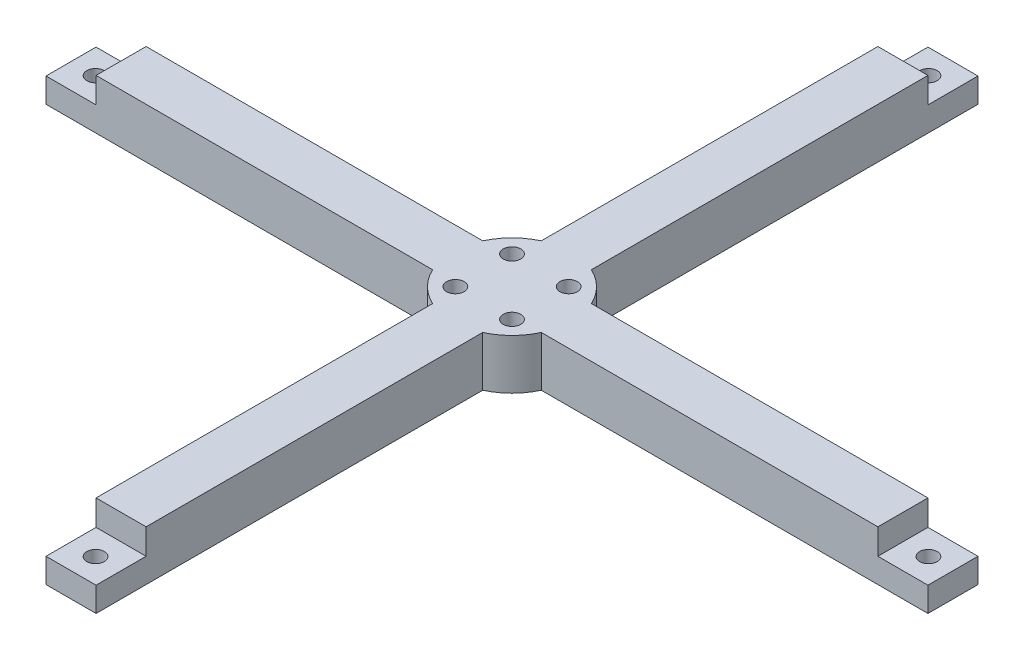
SolidWorks part; units mm, degrees
ref_plane "Front Plane" through (0, 0, 0) normal (0, 0, 1) x (1, 0, 0)
ref_plane "Top Plane" through (0, 0, 0) normal (0, 1, 0) x (1, 0, 0)
ref_plane "Right Plane" through (0, 0, 0) normal (1, 0, 0) x (0, 0, -1)
sketch "Sketch1" plane through (0, 0, 0) normal (0, 1, 0) x (1, 0, 0)
  circle A0 centre (0, 0) radius 11.95
  dimension "D1" = 23.9
extrude "Boss-Extrude1" add sketch "Sketch1" along normal blind 10
sketch "Sketch2" plane through (0, 10, 0) normal (0, 1, 0) x (1, 0, 0)
  line L0 (11.95, 0) -> (98.2, 0) construction
  line L1 (10.8537, -5) -> (98.2, -5)
  line L2 (10.8537, 5) -> (98.2, 5)
  line L4 (98.2, -5) -> (98.2, 5)
  line L5 (0, 5) -> (98.2, 5) construction
  line L6 (0, 0) -> (98.2, 0) construction
  line L7 (0, -5) -> (98.2, -5) construction
  circle A1 centre (0, 0) radius 11.95
  arc A2 (10.8537, -5) -> (10.8537, 5) centre (0, 0) ccw
  point P19 (0, 0)
  dimension "D1" = 98.2
  dimension "D2" = 5
  dimension "D3" = 5
  dimension "D4" = 0
extrude "Boss-Extrude2" add sketch "Sketch2" against normal up to surface (10 mm away) up to face at (0, 0, 11.95)
sketch "Sketch4" plane through (0, 0, 5) normal (0, 0, 1) x (1, 0, 0)
  line L0 (98.2, 0) -> (88.2, 0) construction
  line L1 (98.2, 0) -> (10.8537, 0) construction
  line L2 (88.2, 0) -> (88.2, 5) construction
  line L3 (88.2, 5) -> (78.2, 5) construction
  line L4 (78.2, 5) -> (78.2, 10) construction
  line L5 (10.8537, 10) -> (98.2, 10) construction
  line L6 (88.1, 0) -> (88.1, 4.9)
  line L7 (88.1, 4.9) -> (78.1, 4.9)
  line L8 (78.1, 4.9) -> (78.1, 10)
  line L9 (78.1, 10) -> (98.2, 10)
  line L10 (98.2, 10) -> (98.2, 0)
  line L11 (98.2, 0) -> (88.1, 0)
  dimension "D1" = 10
  dimension "D2" = 10
  dimension "D3" = 5
  dimension "D4" = 0.1
extrude "Cut-Extrude2" cut sketch "Sketch4" against normal through all
sketch "Sketch6" plane through (0, 4.9, 0) normal (0, 1, 0) x (1, 0, 0)
  line L0 (88.1, 5) -> (78.1, 5) construction
  line L1 (78.2, 5) -> (88.2, 5) construction
  line L2 (78.2, 5) -> (78.2, -5) construction
  line L3 (78.2, -5) -> (88.2, -5) construction
  line L4 (88.2, 5) -> (88.2, -5) construction
  line L5 (78.1, -5) -> (88.1, -5) construction
  line L6 (88.1, 5) -> (88.1, -5) construction
  line L7 (78.1, 5) -> (78.1, -5) construction
  line L8 (78.2, 5) -> (88.2, -5) construction
  circle A0 centre (83.2, 0) radius 1.75
  dimension "D3" = 3.5
  dimension "D1" = 0.1
  dimension "D2" = 0.1
extrude "Cut-Extrude4" cut sketch "Sketch6" against normal blind 10
pattern_circular "CirPattern2" count 4 over 360 about axis through (0, 0, 0) along (0, 1, 0) of "Boss-Extrude2", "Cut-Extrude2", "Cut-Extrude4"
sketch "Sketch5" plane through (0, 10, 0) normal (0, 1, 0) x (1, 0, 0)
  line L0 (-8, 0) -> (8, 0) construction
  line L1 (0, -8) -> (0, 8) construction
  line L2 (0, 0) -> (5.6569, 5.6569) construction
  line L3 (0, 0) -> (5.6569, -5.6569) construction
  line L4 (0, 0) -> (-5.6569, -5.6569) construction
  line L5 (0, 0) -> (-5.6569, 5.6569) construction
  circle A0 centre (0, 8) radius 1.75 construction
  circle A1 centre (8, 0) radius 1.75 construction
  circle A2 centre (-8, 0) radius 1.75 construction
  circle A3 centre (0, -8) radius 1.75 construction
  circle A4 centre (0, 0) radius 8 construction
  circle A5 centre (5.6569, 5.6569) radius 1.75
  circle A6 centre (5.6569, -5.6569) radius 1.75
  circle A7 centre (-5.6569, -5.6569) radius 1.75
  circle A8 centre (-5.6569, 5.6569) radius 1.75
  point P4 (0, 0)
  point P5 (0, 0)
  dimension "D3" = 3.5
  dimension "D5" = 3.5
  dimension "D1" = 16
  dimension "D2" = 16
  dimension "D4" = 45
extrude "Cut-Extrude3" cut sketch "Sketch5" against normal through all
